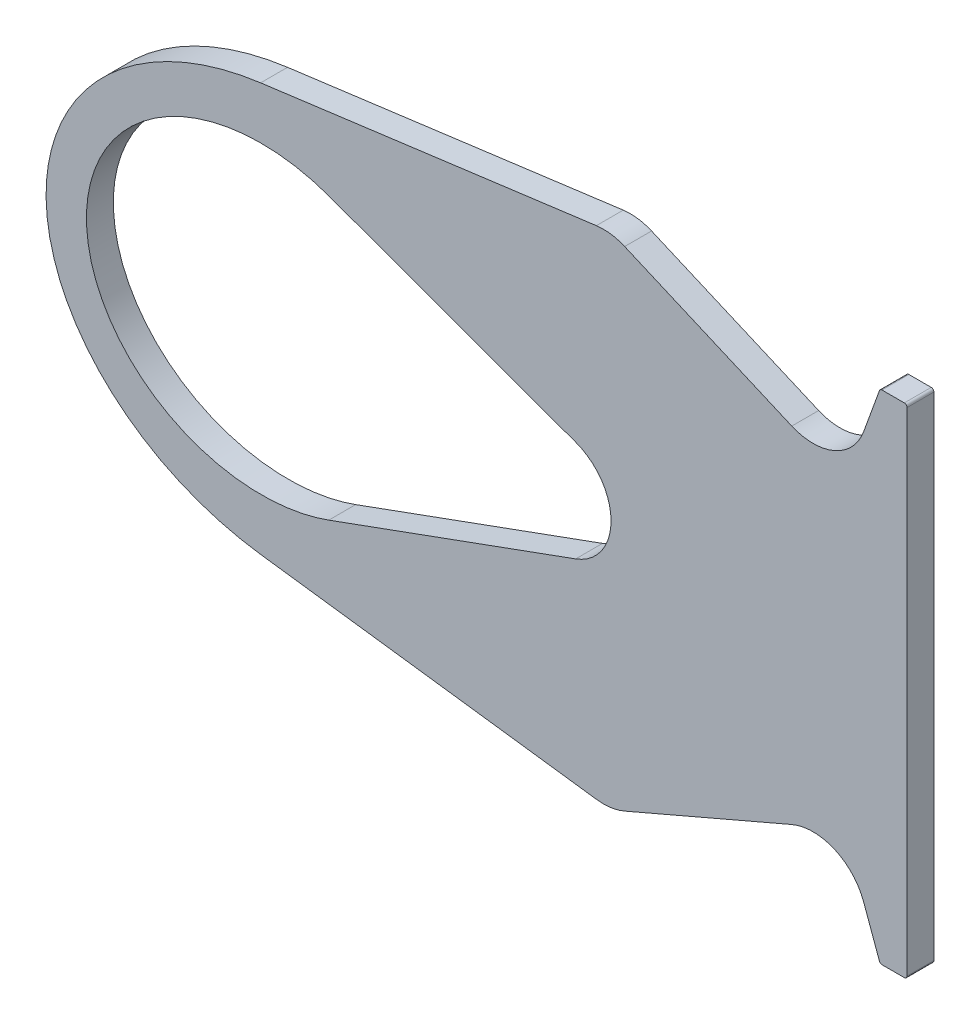
SolidWorks part; units mm, degrees
ref_plane "Plane1" through (0, 0, 0) normal (0, 0, 1) x (1, 0, 0)
ref_plane "Plane2" through (0, 0, 0) normal (0, 1, 0) x (1, 0, 0)
ref_plane "Plane3" through (0, 0, 0) normal (1, 0, 0) x (0, 0, -1)
sketch "Sketch1" plane through (0, 0, 0) normal (0, 0, 1) x (1, 0, 0)
  line L1 (0, 0) -> (-374.0885, 0) construction
  line L30 (-1, -92.5) -> (-9.2998, -92.5)
  line L32 (-10.2395, -91.842) -> (-16.1294, -75.6596)
  line L33 (-42.832, -64.1301) -> (-104.9413, -90.8699)
  line L34 (-115.4605, -92.3289) -> (-240.2509, -75.8999)
  line L35 (-214.9223, -52.1927) -> (-123.1596, -18.7939)
  line L36 (0, -91.5) -> (0, 91.5)
  line L38 (-214.9223, 52.1927) -> (-123.1596, 18.7939)
  line L39 (-115.4605, 92.3289) -> (-240.2509, 75.8999)
  line L40 (-42.832, 64.1301) -> (-104.9413, 90.8699)
  line L41 (-10.2395, 91.842) -> (-16.1294, 75.6596)
  line L42 (-1, 92.5) -> (-9.2998, 92.5)
  arc A0 (-123.1596, -18.7939) -> (-123.1596, 18.7939) centre (-130, 0) ccw
  arc A1 (-115.4605, 92.3289) -> (-104.9413, 90.8699) centre (-112.85, 72.5) cw
  arc A2 (-115.4605, -92.3289) -> (-104.9413, -90.8699) centre (-112.85, -72.5) ccw
  arc A3 (-10.2395, 91.842) -> (-9.2998, 92.5) centre (-9.2998, 91.5) cw
  arc A4 (-1, 92.5) -> (0, 91.5) centre (-1, 91.5) cw
  arc A5 (-1, -92.5) -> (0, -91.5) centre (-1, -91.5) ccw
  arc A6 (-9.2998, -92.5) -> (-10.2395, -91.842) centre (-9.2998, -91.5) cw
  arc A24 (-16.1294, -75.6596) -> (-42.832, -64.1301) centre (-34.9233, -82.5) ccw
  arc A27 (-16.1294, 75.6596) -> (-42.832, 64.1301) centre (-34.9233, 82.5) cw
  ellipse E0 centre (-225, 0) end of major axis (-130, 0) minor radius 76.8973 (-240.2509, 75.8999) -> (-240.2509, -75.8999) ccw
  ellipse E1 centre (-240, 0) end of major axis (-175, 0) minor radius 56.5727 (-214.9223, 52.1927) -> (-214.9223, -52.1927) ccw
  point P7 (-110, 93.0478)
  point P11 (-110, -93.0478)
  point P15 (-10, 92.5)
  point P19 (0, 92.5)
  point P23 (0, -92.5)
  point P29 (-320, 0)
  point P35 (-305, 0)
  dimension "D4" = 20
  dimension "D5" = 185
  dimension "D6" = 30
  dimension "D9" = 1
  dimension "D10" = 110
  dimension "D14" = 320
  dimension "D17" = 65
  dimension "D12" = 95
  dimension "D23" = 20
  dimension "D8" = 20
  dimension "D11" = 130
  dimension "D3" = 185
  dimension "D7" = 10
  dimension "D13" = 40
  dimension "D15" = 15
  dimension "D16" = 15
  dimension "D25" = 20
extrude "Extrude1" add sketch "Sketch1" along normal blind 10
chamfer "Chamfer1" [suppressed] distance 9 angle 45
sketch "Sketch2" [suppressed] plane through (0, 0, 0) normal (1, 0, 0) x (0, 0, -1)
  line L0 (0, 0) -> (-23.4679, 0) construction
  line L1 (-10, 92.5) -> (-2, 92.5) construction
  line L3 (-10, 92.5) -> (-5, 92.5)
  line L4 (-10, -92.5) -> (-10, 92.5) construction
  line L5 (-10, 77.5) -> (-5, 92.5)
  line L6 (-10, 77.5) -> (-10, 92.5)
  line L7 (0, -91.5) -> (0, 91.5) construction
  line L8 (-10, -77.5) -> (-10, -92.5)
  line L9 (-10, -77.5) -> (-5, -92.5)
  line L10 (-10, -92.5) -> (-5, -92.5)
  dimension "D1" = 15
  dimension "D2" = 5
extrude "Cut-Extrude1" [suppressed] cut sketch "Sketch2" against normal blind 20
